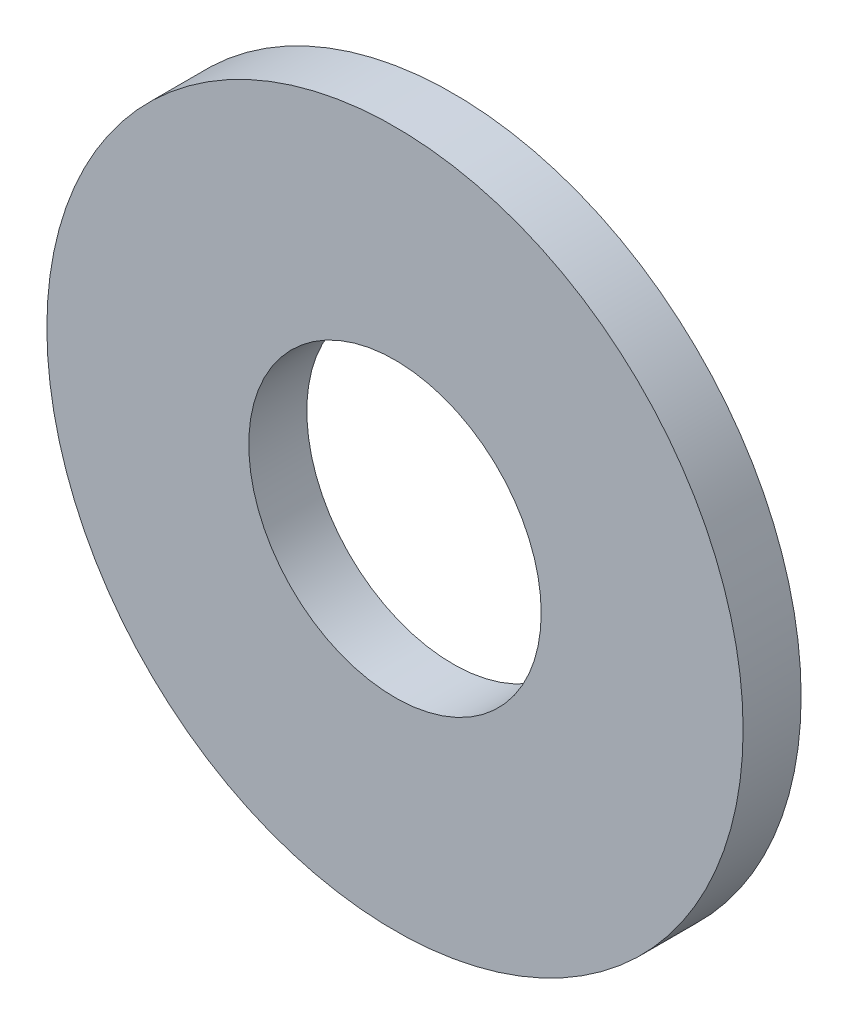
SolidWorks part; units mm, degrees
material "Tin Bearing Bronze"
ref_plane "Front Plane" through (0, 0, 0) normal (0, 0, 1) x (1, 0, 0)
ref_plane "Top Plane" through (0, 0, 0) normal (0, 1, 0) x (1, 0, 0)
ref_plane "Right Plane" through (0, 0, 0) normal (1, 0, 0) x (0, 0, -1)
sketch "Sketch1" plane through (0, 0, 0) normal (0, 0, 1) x (1, 0, 0)
  circle A0 centre (0, 0) radius 4.0005
  circle A1 centre (0, 0) radius 9.525
  dimension "D1" = 8.001
  dimension "D2" = 19.05
extrude "Boss-Extrude1" add sketch "Sketch1" along normal blind 1.5875
